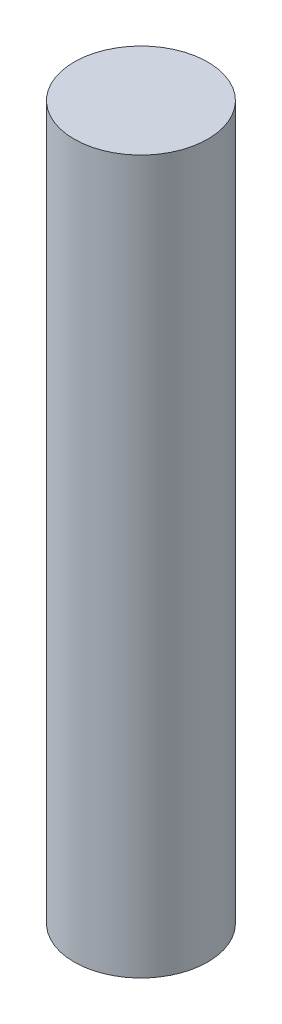
SolidWorks part; units mm, degrees
ref_plane "Front Plane" through (0, 0, 0) normal (0, 0, 1) x (1, 0, 0)
ref_plane "Top Plane" through (0, 0, 0) normal (0, 1, 0) x (1, 0, 0)
ref_plane "Right Plane" through (0, 0, 0) normal (1, 0, 0) x (0, 0, -1)
sketch "Sketch1" plane through (0, 0, 0) normal (0, 1, 0) x (1, 0, 0)
  circle A0 centre (0, 0) radius 4.7625
  dimension "D1" = 9.525
extrude "Boss-Extrude1" add sketch "Sketch1" along normal blind 50.8
